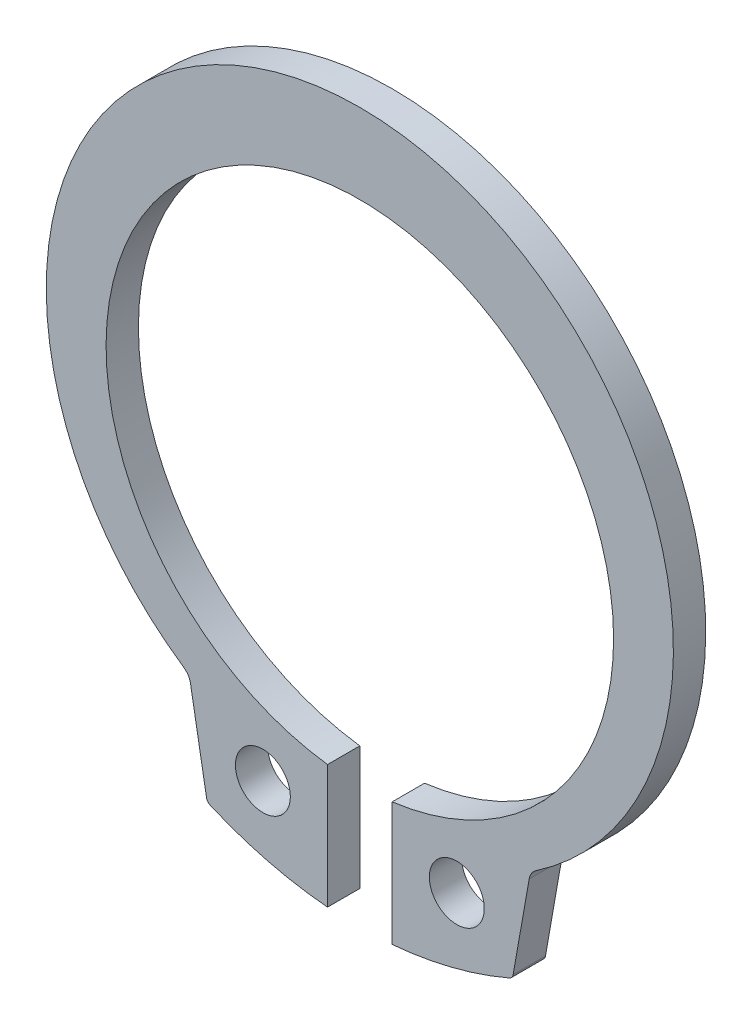
SolidWorks part; units mm, degrees
ref_plane "Front" through (0, 0, 0) normal (0, 0, 1) x (1, 0, 0)
ref_plane "Top" through (0, 0, 0) normal (0, 1, 0) x (1, 0, 0)
ref_plane "Right" through (0, 0, 0) normal (1, 0, 0) x (0, 0, -1)
sketch "Sketch1" plane through (0, 0, 0) normal (0, 0, 1) x (1, 0, 0)
  line L0 (0, 4.2365) -> (0, -4.9012) construction
  line L1 (-1, -8.406) -> (-1, -12.227)
  line L2 (1, -8.406) -> (1, -12.227)
  line L3 (9.7, -0.62) -> (-9.7, -0.62) construction
  line L4 (5.2759, -8.1397) -> (4.7241, -11.2692)
  line L7 (-5.2759, -8.1397) -> (-4.7241, -11.2692)
  line L8 (-5.2759, -8.1397) -> (-5.2759, -16.2104) construction
  arc A0 (1, -8.406) -> (-1, -8.406) centre (0, -0.62) ccw
  arc A1 (5.2759, -8.1397) -> (-5.2759, -8.1397) centre (0, 0) ccw
  arc A2 (-9.7, -0.62) -> (9.7, -0.62) centre (0, -0.62) ccw construction
  arc A3 (4.7241, -11.2692) -> (1, -12.227) centre (0, -0.62) cw
  arc A4 (-4.7241, -11.2692) -> (-1, -12.227) centre (0, -0.62) ccw
  circle A5 centre (3, -9.8444) radius 0.85
  circle A6 centre (-3, -9.8444) radius 0.85
  point P17 (-5, -9.7045)
  dimension "d" = 15.7
  dimension "D2" = 10
  dimension "d0" = 19.4
  dimension "d1" = 1.7
  dimension "R1" = 9.7
  dimension "R" = 11.65
  dimension "B1" = 2
  dimension "C" = 0.62
  dimension "L" = 10
  dimension "B2" = 6
extrude "Body" add sketch "Sketch1" against normal blind 1
fillet "Fillet1" radius 0.2 2 edges at (-4.7241, -11.2692, -0.5) (4.7241, -11.2692, -0.5)
fillet "Fillet2" radius 0.5 2 edges at (5.2759, -8.1397, -0.5) (-5.2759, -8.1397, -0.5)
